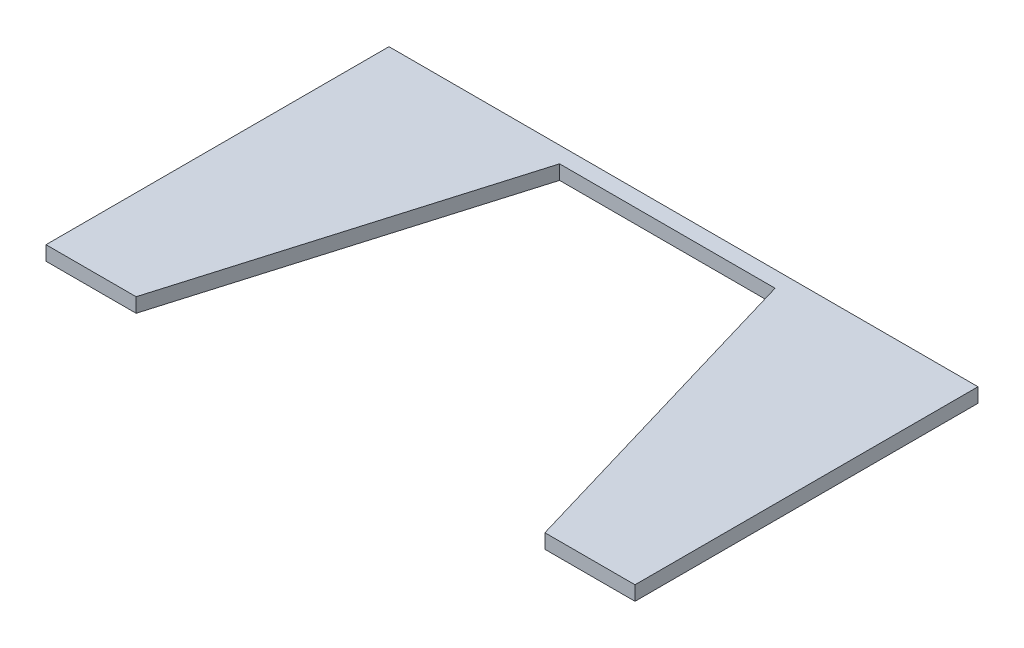
SolidWorks part; units mm, degrees
ref_plane "Front Plane" through (0, 0, 0) normal (0, 0, 1) x (1, 0, 0)
ref_plane "Top Plane" through (0, 0, 0) normal (0, 1, 0) x (1, 0, 0)
ref_plane "Right Plane" through (0, 0, 0) normal (1, 0, 0) x (0, 0, -1)
sketch "Sketch1" plane through (0, 0, 0) normal (0, 1, 0) x (1, 0, 0)
  line L0 (85, -185) -> (30, 1)
  line L1 (-82, 5.5) -> (82, 5.5)
  line L2 (-82, 5.5) -> (-82, -90)
  line L3 (-82, -90) -> (82, -90)
  line L4 (82, 5.5) -> (82, -90)
  line L5 (-82, 5.5) -> (82, -90) construction
  line L6 (-82, -90) -> (82, 5.5) construction
  line L7 (-30, 1) -> (-85, -185)
  line L8 (85, -185) -> (-85, -185)
  line L9 (30, 1) -> (-30, 1)
  line L10 (0, 5.5) -> (0, -90) construction
  point P0 (0, -42.25)
  point P8 (0, 1)
  point P13 (0, -185)
  dimension "D1" = 164
  dimension "D2" = 95.5
  dimension "D3" = 60
  dimension "D4" = 85
  dimension "D5" = 91
  dimension "D6" = 85
  dimension "D7" = 186
extrude "Boss-Extrude1" add sketch "Sketch1" along normal blind 4 contours L9 L0 L3 L4 L1 L2 L7
